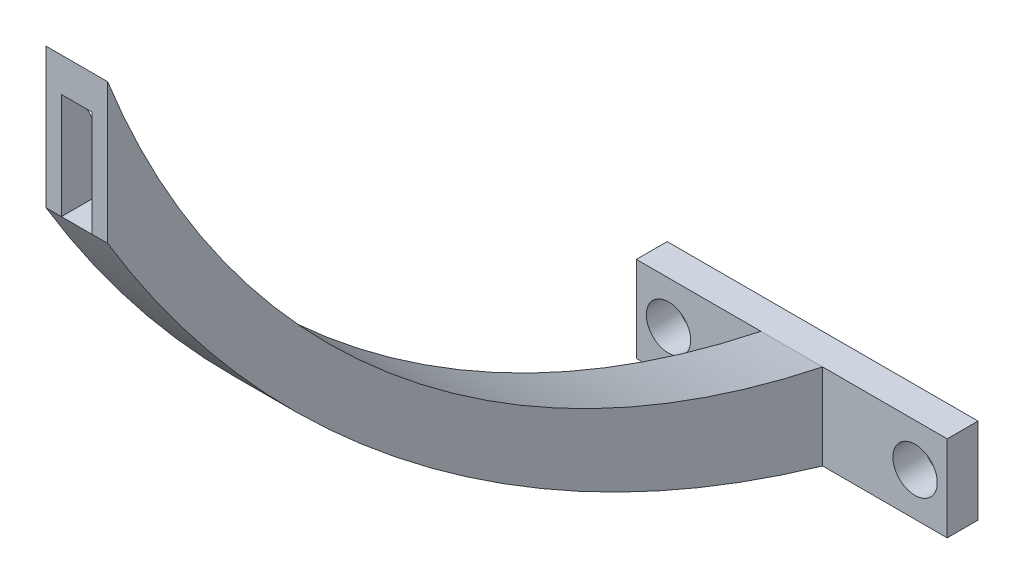
SolidWorks part; units mm, degrees
ref_plane "Front Plane" through (0, 0, 0) normal (0, 0, 1) x (1, 0, 0)
ref_plane "Top Plane" through (0, 0, 0) normal (0, 1, 0) x (1, 0, 0)
ref_plane "Right Plane" through (0, 0, 0) normal (1, 0, 0) x (0, 0, -1)
sketch "Sketch2" plane through (0, 0, 0) normal (0, 1, 0) x (1, 0, 0)
  line L1 (0, 0) -> (6.35, 0)
  line L2 (0, 0) -> (0, -73.66)
  line L3 (0, -73.66) -> (6.35, -73.66)
  line L4 (6.35, 0) -> (6.35, -73.66)
extrude "Boss-Extrude1" add sketch "Sketch2" along normal blind 71.12
sketch "Sketch3" plane through (6.35, 0, 0) normal (1, 0, 0) x (0, 0, -1)
  line L0 (0, 71.12) -> (0, 0) construction
  line L1 (-73.66, 71.12) -> (-73.66, 0) construction
  line L2 (-73.66, 71.12) -> (-73.66, -11.9611)
  line L3 (-73.66, -11.9611) -> (0, -11.9611)
  line L4 (0, -11.9611) -> (0, 71.12)
  line L5 (0, 71.12) -> (-73.66, 71.12)
  arc A0 (-73.66, 71.12) -> (0, 8.8407) centre (20.8044, 108.1468) ccw
  arc A1 (-73.66, 56.6979) -> (0, 0) centre (35.4559, 122.2603) ccw
  line M1 (-73.66, 0) -> (0, 0)
  line M3 (0, 71.12) -> (-73.66, 71.12)
extrude "Cut-Extrude1" cut sketch "Sketch3" against normal blind 71.12 contours A1 L2 M1 | A0 L4 M3
sketch "Sketch4" plane through (0, 0, 73.66) normal (0, 0, 1) x (1, 0, 0)
  line L0 (0, 71.12) -> (1.5875, 71.12)
  line L1 (0, 71.12) -> (6.35, 71.12) construction
  line L2 (1.5875, 71.12) -> (1.5875, 56.6979)
  line L3 (0, 56.6979) -> (6.35, 56.6979) construction
  line L4 (1.5875, 56.6979) -> (3.175, 56.6979)
  line L5 (3.175, 56.6979) -> (3.175, 71.12)
  line L6 (4.7625, 71.12) -> (4.7625, 56.6979)
  line L8 (1.5875, 71.12) -> (4.7625, 71.12)
  line L9 (1.5875, 71.12) -> (1.5875, 56.6979)
  line L10 (1.5875, 56.6979) -> (4.7625, 56.6979)
  line L11 (4.7625, 71.12) -> (4.7625, 56.6979)
  line M3 (0, 56.6979) -> (6.35, 56.6979)
  line M5 (6.35, 71.12) -> (0, 71.12)
extrude "Cut-Extrude2" cut sketch "Sketch4" against normal blind 71.12 contours L5 L2 M3 M5 | L6 L5 M5 M3
sketch "Sketch6" plane through (0, 0, 0) normal (0, 0, -1) x (-1, 0, 0)
  line L0 (-6.35, 0) -> (0, 0) construction
  line L1 (9.6617, 0) -> (-16.0117, 0)
  line L2 (-3.175, 0) -> (-3.175, 8.8407)
  line L3 (9.6617, 8.8407) -> (-16.0117, 8.8407)
  line L4 (-16.0117, 0) -> (-16.0117, 8.8407)
  line L5 (-3.175, 4.4204) -> (-15.875, 4.4204)
  line L6 (9.6617, 8.8407) -> (12.8367, 8.8407)
  line L8 (0, 0) -> (0, 8.8407)
  line L11 (-16.0117, 0) -> (-19.1867, 0)
  line L12 (-16.0117, 0) -> (-16.0117, 8.8407)
  line L13 (-16.0117, 8.8407) -> (-19.1867, 8.8407)
  line L14 (-19.1867, 0) -> (-19.1867, 8.8407)
  line L15 (9.6617, 0) -> (12.8367, 0)
  line L16 (12.8367, 0) -> (12.8367, 8.8407)
  circle A2 centre (-15.875, 4.4204) radius 2.286
  circle A3 centre (9.525, 4.4204) radius 2.286
  line M5 (0, 0) -> (0, 8.8407)
  line M6 (0, 8.8407) -> (-6.35, 8.8407)
  line M7 (-6.35, 8.8407) -> (-6.35, 0)
  line M8 (-6.35, 0) -> (0, 0)
extrude "Boss-Extrude2" add sketch "Sketch6" along normal blind 3.175 contours A2 L4 L13 L14 L11 | A2 L5 L3 L4 M7 | A2 L4 L1 L5 M7 | L15 L16 L6 L3 L1 A3 M5 | L2 L1 M5 M6 | L2 L5 M7 M8 | L5 L2 M6 M7
sketch "Sketch7" plane through (1.5875, 0, 0) normal (1, 0, 0) x (0, 0, -1)
  line L0 (-73.66, 67.5962) -> (-72.2018, 67.5962)
  line L1 (-73.66, 71.12) -> (-73.66, 56.6979) construction
  line L2 (-73.66, 67.5962) -> (-73.66, 71.12)
  line L3 (-73.66, 71.12) -> (-72.2018, 67.5962)
  arc A0 (-73.66, 71.12) -> (-66.6457, 56.6979) centre (20.8044, 108.1468) ccw construction
extrude "Boss-Extrude3" add sketch "Sketch7" along normal up to surface (3.175 mm away) up to face at (4.7625, 61.459, 71.417)
